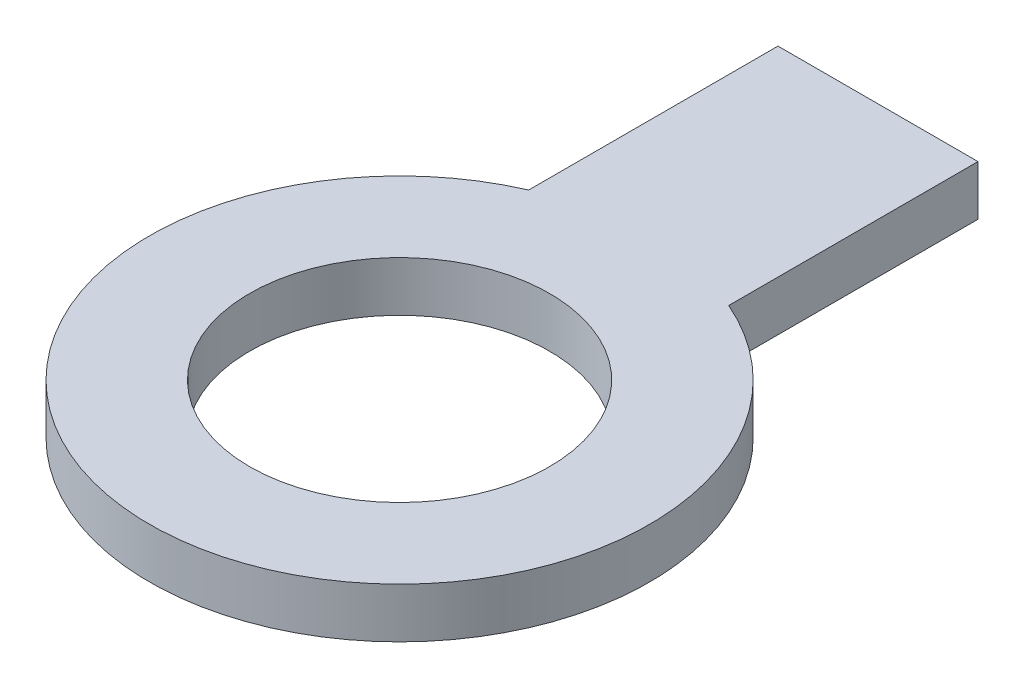
SolidWorks part; units mm, degrees
ref_plane "Front Plane" through (0, 0, 0) normal (0, 0, 1) x (1, 0, 0)
ref_plane "Top Plane" through (0, 0, 0) normal (0, 1, 0) x (1, 0, 0)
ref_plane "Right Plane" through (0, 0, 0) normal (1, 0, 0) x (0, 0, -1)
sketch "Sketch1" plane through (0, 0, 0) normal (0, 1, 0) x (1, 0, 0)
  circle A0 centre (0, 0) radius 10
  dimension "D1" = 20
sketch "Sketch2" plane through (0, 0, 0) normal (0, 1, 0) x (1, 0, 0)
  line L1 (4, 9.1652) -> (-4, 9.1652)
  line L2 (4, 9.1652) -> (4, 19.1352)
  line L3 (4, 19.1352) -> (-4, 19.1352)
  line L4 (-4, 9.1652) -> (-4, 19.1352)
  circle A0 centre (0, 0) radius 10 construction
  dimension "D1" = 8
  dimension "D2" = 9.97
  dimension "D3" = 4
extrude "Boss-Extrude1" add sketch "Sketch1" against normal blind 2
extrude "Boss-Extrude2" add sketch "Sketch2" against normal blind 2
sketch "Sketch3" plane through (0, 0, 0) normal (0, 1, 0) x (1, 0, 0)
  circle A0 centre (0, 0) radius 6
  dimension "D1" = 12
extrude "Cut-Extrude1" cut sketch "Sketch3" against normal through all
